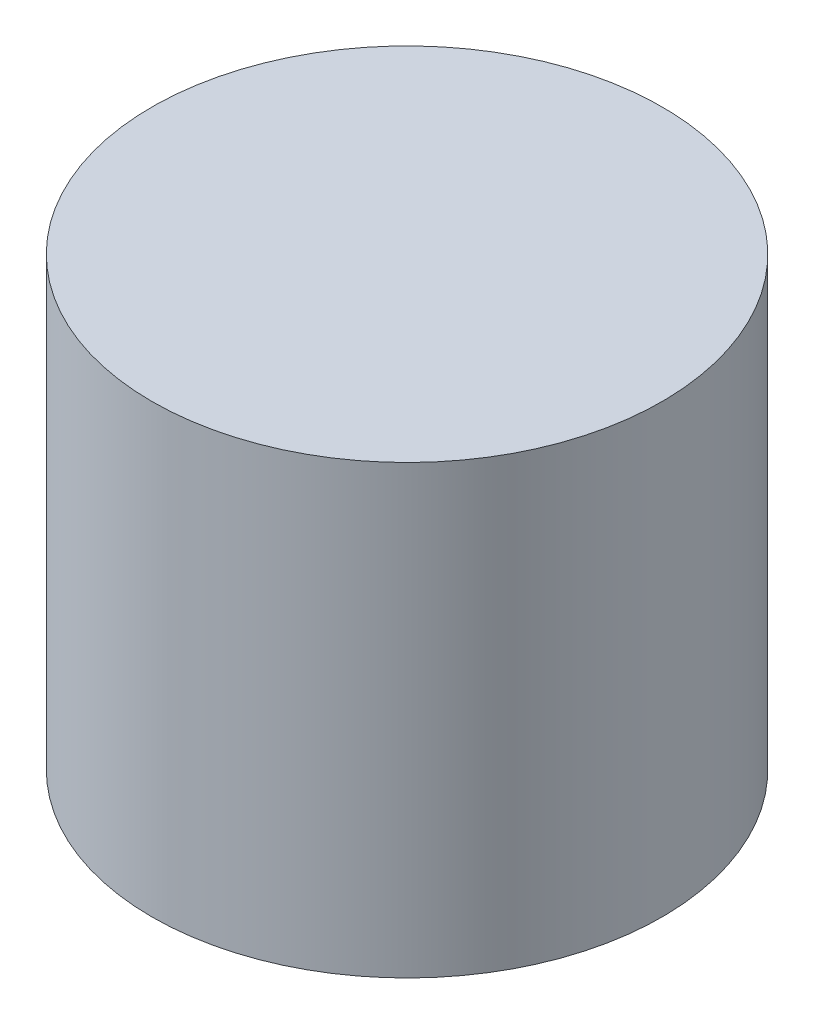
SolidWorks part; units mm, degrees
ref_plane "Спереди" through (0, 0, 0) normal (0, 0, 1) x (1, 0, 0)
ref_plane "Сверху" through (0, 0, 0) normal (0, 1, 0) x (1, 0, 0)
ref_plane "Справа" through (0, 0, 0) normal (1, 0, 0) x (0, 0, -1)
other "Configuration Table"
sketch "Эскиз1" plane through (0, 0, 0) normal (0, 1, 0) x (1, 0, 0)
  circle A0 centre (-1.1023, 0.3432) radius 4
  dimension "D1" = 8
extrude "Бобышка-Вытянуть2" add sketch "Эскиз1" along normal blind 7
